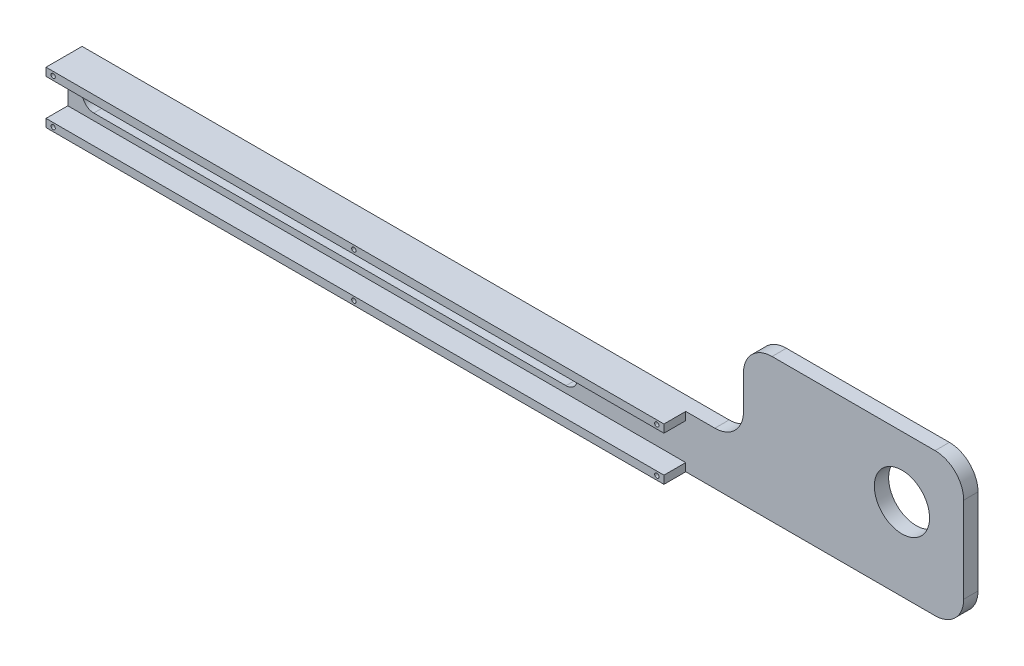
SolidWorks part; units mm, degrees
ref_plane "Front Plane" through (0, 0, 0) normal (0, 0, 1) x (1, 0, 0)
ref_plane "Top Plane" through (0, 0, 0) normal (0, 1, 0) x (1, 0, 0)
ref_plane "Right Plane" through (0, 0, 0) normal (1, 0, 0) x (0, 0, -1)
sketch "Sketch1" plane through (0, 0, 0) normal (0, 0, 1) x (1, 0, 0)
  line L0 (0, 0) -> (236.22, 0)
  line L1 (0, 0) -> (0, 18.288)
  line L2 (0, 18.288) -> (236.22, 18.288)
  line L3 (236.22, 18.288) -> (236.22, 0)
  line L4 (9.08, 9.144) -> (174.18, 9.144) construction
  line L5 (236.22, 0) -> (313.22, 0)
  line L6 (236.22, 0) -> (236.22, 50)
  line L7 (236.22, 50) -> (313.22, 50)
  line L8 (313.22, 0) -> (313.22, 50)
  line L9 (9.08, 13.144) -> (174.18, 13.144)
  line L10 (9.08, 5.144) -> (174.18, 5.144)
  line L11 (78.6872, 13.144) -> (78.6872, 18.288) construction
  line L12 (78.6872, 5.144) -> (78.6872, 0) construction
  arc A0 (9.08, 13.144) -> (9.08, 5.144) centre (9.08, 9.144) ccw
  arc A1 (174.18, 5.144) -> (174.18, 13.144) centre (174.18, 9.144) ccw
  circle A2 centre (291.63, 28.638) radius 9.652
  point P10 (91.63, 9.144)
  point P19 (5.08, 9.144)
  dimension "D5" = 4
  dimension "D7" = 5.08
  dimension "D8" = 19.304
  dimension "D10" = 200
  dimension "D1" = 236.22
  dimension "D2" = 18.288
  dimension "D3" = 21.59
  dimension "D4" = 50
  dimension "D6" = 165.1
  dimension "D9" = 15.494
  dimension "D11" = 8
extrude "Boss-Extrude1" add sketch "Sketch1" along normal blind 5 contours L3 L2 L1 L0 A1 L10 A0 L9 | L5 L8 L7 L6 L3 A2
fillet "Fillet1" radius 10 4 edges at (313.22, 0, 2.5) (313.22, 50, 2.5) (236.22, 50, 2.5) (236.22, 18.288, 2.5)
sketch "Sketch2" plane through (0, 0, 5) normal (0, 0, 1) x (1, 0, 0)
  line L0 (4.0714, 0) -> (4.0714, 18.288) construction
  line L1 (0, 18.288) -> (216.0439, 18.288)
  line L2 (0, 18.288) -> (0, 15.494)
  line L3 (0, 15.494) -> (216.0439, 15.494)
  line L4 (216.0439, 18.288) -> (216.0439, 15.494)
  line L5 (0, 0) -> (216.0439, 0)
  line L6 (0, 0) -> (0, 2.794)
  line L7 (0, 2.794) -> (216.0439, 2.794)
  line L8 (216.0439, 0) -> (216.0439, 2.794)
  line L9 (0.9681, 15.494) -> (0.9681, 2.794) construction
  line L10 (4.0714, 9.144) -> (-17.0148, 9.144) construction
  line L12 (-17.0148, 9.144) -> (-12.3997, 24.7118) construction
  line L13 (9.08, 5.144) -> (174.18, 5.144) construction
  point P19 (0.9681, 9.144)
  dimension "D2" = 12.7
  dimension "D3" = 2.35
extrude "Boss-Extrude2" add sketch "Sketch2" along normal blind 7.62
sketch "Sketch3" plane through (0, 0, 12.62) normal (0, 0, 1) x (1, 0, 0)
  line L0 (0, 18.288) -> (0, 15.494) construction
  line L1 (216.0439, 15.494) -> (216.0439, 18.288) construction
  line L2 (0, 9.144) -> (9.428, 9.144)
  line L3 (0, 2.794) -> (0, 15.494) construction
  circle A0 centre (2.5, 16.891) radius 0.75
  circle A1 centre (107.6322, 16.891) radius 0.75
  circle A2 centre (213.5439, 16.891) radius 0.75
  circle A3 centre (213.5439, 1.397) radius 0.75
  circle A4 centre (107.6322, 1.397) radius 0.75
  circle A5 centre (2.5, 1.397) radius 0.75
  dimension "D1" = 1.5
  dimension "D3" = 1.5
  dimension "D4" = 1.5
  dimension "D2" = 2.5
  dimension "D5" = 2.5
extrude "Cut-Extrude1" cut sketch "Sketch3" against normal blind 5 contours A0 | A5 | A1 | A4 | A2 | A3
